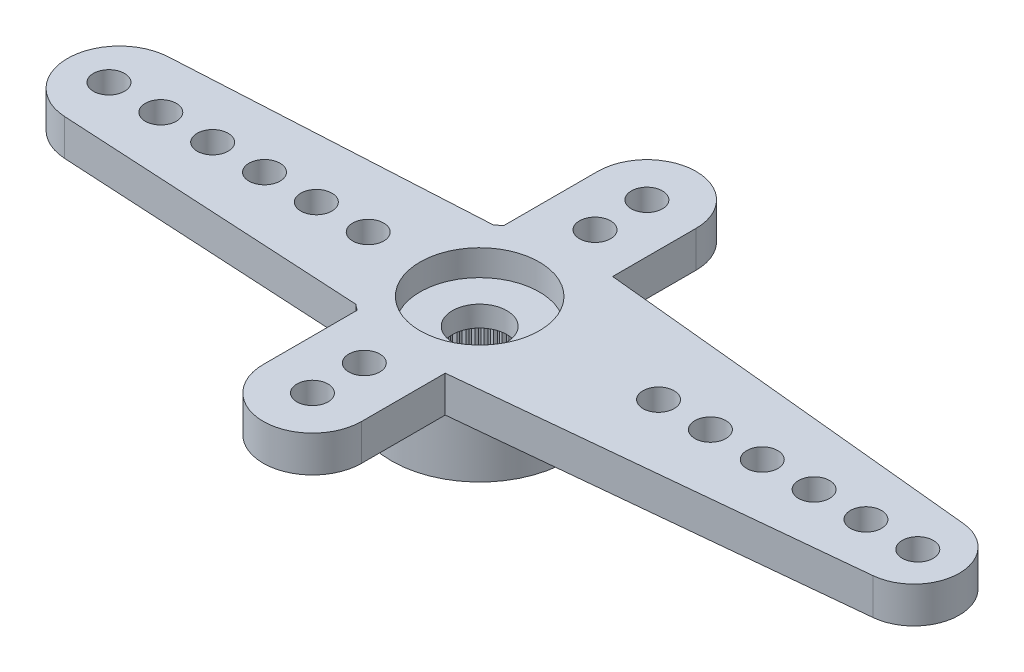
SolidWorks part; units mm, degrees
material "PVC Rígido"
ref_plane "Plano frontal" through (0, 0, 0) normal (0, 0, 1) x (1, 0, 0)
ref_plane "Plano superior" through (0, 0, 0) normal (0, 1, 0) x (1, 0, 0)
ref_plane "Plano direito" through (0, 0, 0) normal (1, 0, 0) x (0, 0, -1)
sketch "Esboço1" plane through (0, 0, 0) normal (0, 1, 0) x (1, 0, 0)
  line L0 (0, 0) -> (-13.9, 0) construction
  line L1 (-14.0098, 1.997) -> (-2.1301, 2.65)
  line L2 (-2.1301, -2.65) -> (-14.0098, -1.997)
  line L3 (-1.9, -5.618) -> (-1.9, 8.7023) construction
  arc A0 (-2.1301, -2.65) -> (-2.1301, 2.65) centre (0, 0) ccw
  arc A1 (-14.0098, 1.997) -> (-14.0098, -1.997) centre (-13.9, 0) ccw
  circle A2 centre (0, 0) radius 1.997
  dimension "D1" = 6.8
  dimension "D2" = 4
  dimension "D3" = 3.994
  dimension "D6" = 14
  dimension "D4" = 5.3
  dimension "D5" = 1.9
extrude "Ressalto-extrusão1" add sketch "Esboço1" against normal blind 1.4
sketch "Esboço2" plane through (0, -1.4, 0) normal (0, -1, 0) x (1, 0, 0)
  arc A0 (-2.1301, -2.65) -> (-2.1301, 2.65) centre (0, 0) ccw construction
  circle A1 centre (0, 0) radius 3.4
extrude "Ressalto-extrusão2" add sketch "Esboço2" along normal offset from surface (2.4 mm away) 3.8 up to face at (0, 0, 1.997)
hole_wizard "Furo1" positions "Esboço9" profile "Esboço10" legacy end condition through all
sketch "Esboço9" plane through (0, 0, 0) normal (0, 1, 0) x (1, 0, 0)
  line L1 (-14.3, 0) -> (0, 0) construction
  arc A2 (-14.0098, 1.997) -> (-14.0098, -1.997) centre (-13.9, 0) ccw construction
  point P0 (-14.3, 0)
  point P19 (-15.9, 0)
  dimension "D1" = 1.6
sketch "Esboço10" plane through (-14.3, 0, 0) normal (1, 0, 0) x (0, 0, 1)
  line L0 (0, 0) -> (0, 3.8)
  line L1 (0, 3.8) -> (0.6, 3.8)
  line L2 (0.6, 3.8) -> (0.6, 0)
  line L3 (0.6, 0) -> (0, 0)
  line L4 (0, 110) -> (0, -10) construction
  dimension "Diameter" = 1.2
  dimension "Depth" = 3.8
pattern_linear "Padrão linear1" count 6 spacing 2 along (1, 0, 0) of "Furo1"
sketch "Esboço12" plane through (0, 0, 0) normal (0, 1, 0) x (1, 0, 0)
  line L0 (0.3349, 3.3835) -> (16.9224, 1.7415)
  line L1 (16.9224, -1.7415) -> (0.3349, -3.3835)
  line L2 (1.9, 10.7119) -> (1.9, -11.0008) construction
  arc A0 (-2.1301, -2.65) -> (-2.1301, 2.65) centre (0, 0) ccw construction
  arc A1 (0.3349, -3.3835) -> (0.3349, 3.3835) centre (0, 0) ccw
  arc A2 (16.9224, 1.7415) -> (16.9224, -1.7415) centre (16.75, 0) cw
  dimension "D1" = 1.75
  dimension "D2" = 1.9
  dimension "D3" = 16.6
extrude "Ressalto-extrusão3" add sketch "Esboço12" against normal up to surface (1.4 mm away) up to face at (-12.3, -1.4, 0.6)
hole_wizard "Furo2" positions "Esboço13" profile "Esboço14" legacy end condition through all
sketch "Esboço13" plane through (0, 0, 0) normal (0, 1, 0) x (1, 0, 0)
  line L0 (0, 0) -> (16.9, 0) construction
  arc A0 (16.9224, -1.7415) -> (16.9224, 1.7415) centre (16.75, 0) ccw construction
  point P0 (16.9, 0)
  point P6 (18.5, 0)
  dimension "D1" = 1.6
sketch "Esboço14" plane through (16.9, 0, 0) normal (1, 0, 0) x (0, 0, 1)
  line L0 (0, 0) -> (0, 3.8)
  line L1 (0, 3.8) -> (0.6, 3.8)
  line L2 (0.6, 3.8) -> (0.6, 0)
  line L3 (0.6, 0) -> (0, 0)
  line L4 (0, 110) -> (0, -10) construction
  dimension "Diameter" = 1.2
  dimension "Depth" = 3.8
pattern_linear "Padrão linear2" count 6 spacing 2 along (-1, 0, 0) of "Furo2"
sketch "Esboço16" plane through (0, 0, 0) normal (0, 1, 0) x (1, 0, 0)
  line L0 (0, -6.45) -> (0, 6.45) construction
  line L1 (-1.9, -6.45) -> (-1.9, 6.45)
  line L2 (1.9, -6.45) -> (1.9, 6.45)
  arc A0 (-1.9, -6.45) -> (1.9, -6.45) centre (0, -6.45) ccw
  arc A1 (1.9, 6.45) -> (-1.9, 6.45) centre (0, 6.45) ccw
  circle A2 centre (0, 0) radius 1.997 construction
  arc A3 (-1.9, 0.6149) -> (-1.9, -0.6149) centre (0, 0) ccw
  arc A4 (1.9, -0.6149) -> (1.9, 0.6149) centre (0, 0) ccw
  point P2 (0, 0)
  circle M26 centre (0, 0) radius 1.997
  dimension "D2" = 16.7
  dimension "D1" = 3.8
extrude "Ressalto-extrusão4" add sketch "Esboço16" against normal up to surface (1.4 mm away) contours L1 M26 | L2 M26
hole_wizard "Furo3" positions "Esboço17" profile "Esboço18" legacy end condition through all
sketch "Esboço17" plane through (0, 0, 0) normal (0, 1, 0) x (1, 0, 0)
  point P0 (0, -6.45)
sketch "Esboço18" plane through (0, 0, 6.45) normal (1, 0, 0) x (0, 0, 1)
  line L0 (0, 0) -> (0, 3.8)
  line L1 (0, 3.8) -> (0.6, 3.8)
  line L2 (0.6, 3.8) -> (0.6, 0)
  line L3 (0.6, 0) -> (0, 0)
  line L4 (0, 110) -> (0, -10) construction
  dimension "Diameter" = 1.2
  dimension "Depth" = 3.8
pattern_linear "Padrão linear3" count 2 spacing 2 along (0, 0, -1) of "Furo3"
pattern_circular "PadrãoCircular1" count 2 over 360 about axis through (0, 0, 0) along (0, 1, 0) of "Padrão linear3", "Furo3"
hole_wizard "Furo4" positions "Esboço3" profile "Esboço4" legacy
sketch "Esboço3" plane through (0, -3.8, 0) normal (0, -1, 0) x (-1, 0, 0)
  point P0 (0, 0)
sketch "Esboço4" plane through (0, -3.8, 0) normal (1, 0, 0) x (0, 0, -1)
  line L0 (0, 0) -> (0, 2)
  line L1 (0, 2) -> (2.475, 2)
  line L2 (2.475, 2) -> (2.475, 0)
  line L3 (2.475, 0) -> (0, 0)
  line L4 (0, 110) -> (0, -10) construction
  dimension "Diameter" = 4.95
  dimension "Depth" = 2
hole_wizard "Furo5" positions "Esboço5" profile "Esboço6" legacy
sketch "Esboço5" plane through (0, 0, 0) normal (0, 1, 0) x (1, 0, 0)
  point P0 (0, 0)
sketch "Esboço6" plane through (0, 0, 0) normal (1, 0, 0) x (0, 0, 1)
  line L0 (0, 0) -> (0, 1)
  line L1 (0, 1) -> (2.3, 1)
  line L2 (2.3, 1) -> (2.3, 0)
  line L3 (2.3, 0) -> (0, 0)
  line L4 (0, 110) -> (0, -10) construction
  dimension "Diameter" = 4.6
  dimension "Depth" = 1
hole_wizard "Furo6" positions "Esboço7" profile "Esboço8" legacy end condition through all
sketch "Esboço7" plane through (0, 0, 0) normal (0, 1, 0) x (1, 0, 0)
  point P0 (0, 0)
sketch "Esboço8" plane through (0, 0, 0) normal (1, 0, 0) x (0, 0, 1)
  line L0 (0, 0) -> (0, 3.8)
  line L1 (0, 3.8) -> (1.05, 3.8)
  line L2 (1.05, 3.8) -> (1.05, 0)
  line L3 (1.05, 0) -> (0, 0)
  line L4 (0, 110) -> (0, -10) construction
  dimension "Diameter" = 2.1
  dimension "Depth" = 3.8
sketch "Esboço11" plane through (0, -3.8, 0) normal (0, -1, 0) x (1, 0, 0)
  line L0 (-0.0981, 2.4731) -> (0, 2.375)
  line L1 (0, 2.375) -> (0.0981, 2.4731)
  line L2 (0, 0) -> (0, 2.475) construction
  circle A0 centre (0, 0) radius 2.375 construction
  circle A1 centre (0, 0) radius 2.475
  arc A2 (0.0981, 2.4731) -> (-0.0981, 2.4731) centre (0, 0) ccw
  dimension "D3" = 4.75
  dimension "D2" = 0.1
  dimension "D1" = 0
extrude "Ressalto-extrusão5" add sketch "Esboço11" against normal up to surface (2 mm away) up to face at (0, -1.8, 1.05)
pattern_circular "PadrãoCircular2" count 60 over 360 about axis through (0, 0, 0) along (0, 1, 0) of "Ressalto-extrusão5"
sketch "Sketch1" plane through (0, 0, 0) normal (0, 1, 0) x (1, 0, 0)
  line L8 (-1.9, 6.45) -> (-1.9, 2.8196)
  line L9 (-2.1301, 2.65) -> (-14.0098, 1.997)
  line L10 (-14.0098, -1.997) -> (-2.1301, -2.65)
  line L11 (-1.9, 6.45) -> (-1.9, 2.8196)
  line L12 (-1.9, -2.8196) -> (-1.9, -6.45)
  line L13 (1.9, -3.2285) -> (16.9224, -1.7415)
  line L14 (16.9224, 1.7415) -> (1.9, 3.2285)
  line L15 (-1.9, -2.8196) -> (-1.9, -6.45)
  line L17 (-2.1301, 2.65) -> (-14.0098, 1.997)
  line L18 (-14.0098, -1.997) -> (-2.1301, -2.65)
  line L21 (1.9, -3.2285) -> (16.9224, -1.7415)
  line L22 (16.9224, 1.7415) -> (1.9, 3.2285)
  line L24 (1.9, -6.45) -> (1.9, -3.2285)
  line L25 (1.9, -6.45) -> (1.9, -3.2285)
  line L26 (1.9, 3.2285) -> (1.9, 6.45)
  line L27 (1.9, 3.2285) -> (1.9, 6.45)
  circle A0 centre (0, 0) radius 3.4 construction
  circle A1 centre (0, 0) radius 3.4
  arc A6 (-1.9, 2.8196) -> (-2.1301, 2.65) centre (0, 0) ccw
  arc A7 (-14.0098, 1.997) -> (-14.0098, -1.997) centre (-13.9, 0) ccw
  arc A8 (-2.1301, -2.65) -> (-1.9, -2.8196) centre (0, 0) ccw
  arc A10 (16.9224, -1.7415) -> (16.9224, 1.7415) centre (16.75, 0) ccw
  arc A12 (-1.9, 2.8196) -> (-2.1301, 2.65) centre (0, 0) ccw
  arc A13 (-14.0098, 1.997) -> (-14.0098, -1.997) centre (-13.9, 0) ccw
  arc A14 (-2.1301, -2.65) -> (-1.9, -2.8196) centre (0, 0) ccw
  arc A16 (16.9224, -1.7415) -> (16.9224, 1.7415) centre (16.75, 0) ccw
  arc A19 (-1.9, -6.45) -> (1.9, -6.45) centre (0, -6.45) ccw
  arc A20 (-1.9, -6.45) -> (1.9, -6.45) centre (0, -6.45) ccw
  arc A21 (1.9, 6.45) -> (-1.9, 6.45) centre (0, 6.45) ccw
  arc A22 (1.9, 6.45) -> (-1.9, 6.45) centre (0, 6.45) ccw
  dimension "D1" = 0
